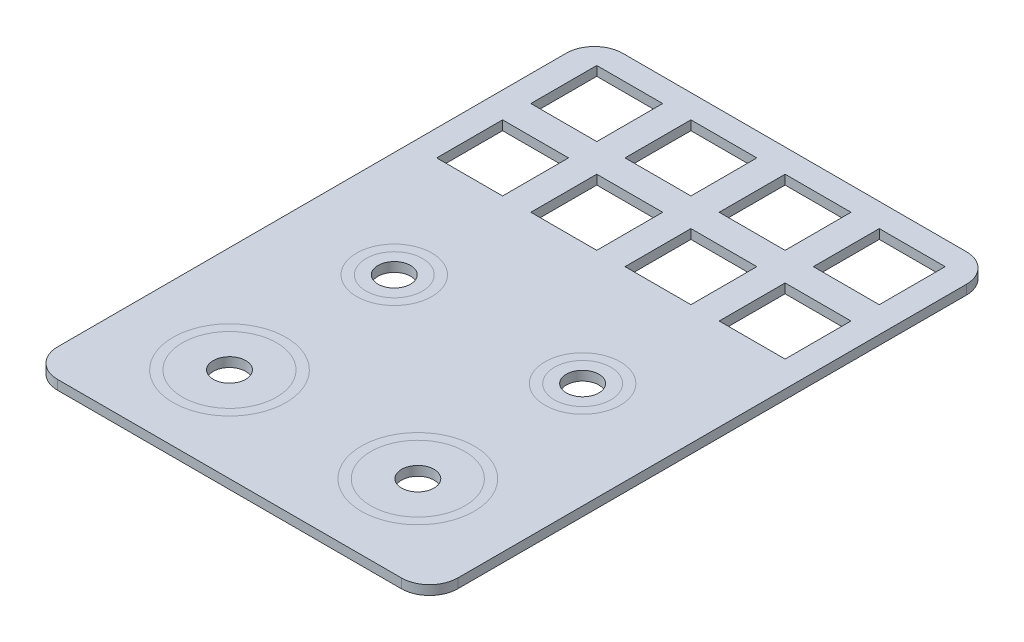
SolidWorks part; units mm, degrees
ref_plane "Plan de face" through (0, 0, 0) normal (0, 0, 1) x (1, 0, 0)
ref_plane "Plan de dessus" through (0, 0, 0) normal (0, 1, 0) x (1, 0, 0)
ref_plane "Plan de droite" through (0, 0, 0) normal (1, 0, 0) x (0, 0, -1)
sketch "Esquisse1" plane through (0, 0, 0) normal (0, 1, 0) x (1, 0, 0)
  line L1 (-42.5, -60) -> (42.5, -60)
  line L2 (-42.5, -60) -> (-42.5, 60)
  line L3 (-42.5, 60) -> (42.5, 60)
  line L4 (42.5, -60) -> (42.5, 60)
  line L5 (-42.5, -60) -> (42.5, 60) construction
  line L6 (-42.5, 60) -> (42.5, -60) construction
  point P0 (0, 0)
  dimension "D1" = 85
  dimension "D2" = 120
extrude "Boss.-Extru.1" add sketch "Esquisse1" along normal blind 2
sketch "Esquisse2" plane through (0, 2, 0) normal (0, 1, 0) x (1, 0, 0)
  line L0 (42.5, 60) -> (-42.5, 60) construction
  line L1 (-37, 55) -> (-23, 55)
  line L2 (-37, 55) -> (-37, 41)
  line L3 (-37, 41) -> (-23, 41)
  line L4 (-23, 55) -> (-23, 41)
  line L5 (-37, 55) -> (-23, 41) construction
  line L6 (-37, 41) -> (-23, 55) construction
  line L7 (-17, 55) -> (-3, 55)
  line L8 (-17, 55) -> (-17, 41)
  line L9 (-17, 41) -> (-3, 41)
  line L10 (-3, 55) -> (-3, 41)
  line L11 (-17, 55) -> (-3, 41) construction
  line L12 (-17, 41) -> (-3, 55) construction
  line L13 (3, 55) -> (17, 55)
  line L14 (3, 55) -> (3, 41)
  line L15 (3, 41) -> (17, 41)
  line L16 (17, 55) -> (17, 41)
  line L17 (3, 55) -> (17, 41) construction
  line L18 (3, 41) -> (17, 55) construction
  line L19 (23, 55) -> (37, 55)
  line L20 (23, 55) -> (23, 41)
  line L21 (23, 41) -> (37, 41)
  line L22 (37, 55) -> (37, 41)
  line L23 (23, 55) -> (37, 41) construction
  line L24 (23, 41) -> (37, 55) construction
  line L25 (23, 35) -> (37, 35)
  line L26 (23, 35) -> (23, 21)
  line L27 (23, 21) -> (37, 21)
  line L28 (37, 35) -> (37, 21)
  line L29 (23, 35) -> (37, 21) construction
  line L30 (23, 21) -> (37, 35) construction
  line L31 (17, 35) -> (3, 35)
  line L32 (17, 35) -> (17, 21)
  line L33 (17, 21) -> (3, 21)
  line L34 (3, 35) -> (3, 21)
  line L35 (17, 35) -> (3, 21) construction
  line L36 (17, 21) -> (3, 35) construction
  line L37 (-3, 35) -> (-17, 35)
  line L38 (-3, 35) -> (-3, 21)
  line L39 (-3, 21) -> (-17, 21)
  line L40 (-17, 35) -> (-17, 21)
  line L41 (-3, 35) -> (-17, 21) construction
  line L42 (-3, 21) -> (-17, 35) construction
  line L43 (-37, 35) -> (-23, 35)
  line L44 (-37, 35) -> (-37, 21)
  line L45 (-37, 21) -> (-23, 21)
  line L46 (-23, 35) -> (-23, 21)
  line L47 (-37, 35) -> (-23, 21) construction
  line L48 (-37, 21) -> (-23, 35) construction
  point P0 (-30, 48)
  point P5 (-10, 48)
  point P10 (10, 48)
  point P15 (30, 48)
  point P20 (30, 28)
  point P25 (10, 28)
  point P30 (-10, 28)
  point P35 (-30, 28)
  dimension "D1" = 14
  dimension "D2" = 14
  dimension "D3" = 20
  dimension "D4" = 20
  dimension "D5" = 20
  dimension "D6" = 10
  dimension "D7" = 12
  dimension "D8" = 20
extrude "Enlèv. mat.-Extru.1" cut sketch "Esquisse2" against normal blind 2
sketch "Esquisse3" plane through (0, 2, 0) normal (0, 1, 0) x (1, 0, 0)
  circle A0 centre (-20, -5) radius 8
  circle A1 centre (-20, -40) radius 12
  circle A2 centre (20, -5) radius 8
  circle A3 centre (20, -40) radius 12
  dimension "D1" = 16
  dimension "D6" = 24
  dimension "D2" = 35
  dimension "D3" = 20
  dimension "D4" = 20
  dimension "D5" = 5
extrude "Enlèv. mat.-Extru.2" cut sketch "Esquisse3" against normal blind 2
fillet "Congé1" radius 6 4 edges at (42.5, 1, 60) (-42.5, 1, 60) (-42.5, 1, -60) (42.5, 1, -60)
sketch "Esquisse4" plane through (0, 2, 0) normal (0, 1, 0) x (1, 0, 0)
  circle A0 centre (-20, -5) radius 8 construction
  circle A1 centre (-20, -5) radius 8
  circle A2 centre (-20, -40) radius 12 construction
  circle A3 centre (20, -40) radius 12 construction
  circle A4 centre (20, -5) radius 8 construction
  circle A5 centre (-20, -40) radius 12
  circle A6 centre (20, -40) radius 12
  circle A7 centre (20, -5) radius 8
  circle A8 centre (-20, -5) radius 6
  circle A9 centre (20, -5) radius 6
  circle A10 centre (20, -40) radius 10
  circle A11 centre (-20, -40) radius 10
  dimension "D1" = 2
extrude "Boss.-Extru.2" add sketch "Esquisse4" against normal blind 2 separate body
sketch "Esquisse5" plane through (0, 2, 0) normal (0, 1, 0) x (1, 0, 0)
  circle A0 centre (-20, -40) radius 10 construction
  circle A1 centre (20, -40) radius 10 construction
  circle A2 centre (20, -5) radius 6 construction
  circle A3 centre (-20, -5) radius 6 construction
  circle A4 centre (-20, -40) radius 10
  circle A5 centre (20, -40) radius 10
  circle A6 centre (20, -5) radius 6
  circle A7 centre (-20, -5) radius 6
  circle A8 centre (-20, -5) radius 3.45
  circle A9 centre (20, -5) radius 3.45
  circle A10 centre (20, -40) radius 3.45
  circle A11 centre (-20, -40) radius 3.45
  dimension "D1" = 6.9
extrude "Boss.-Extru.4" add sketch "Esquisse5" against normal blind 2 separate body
